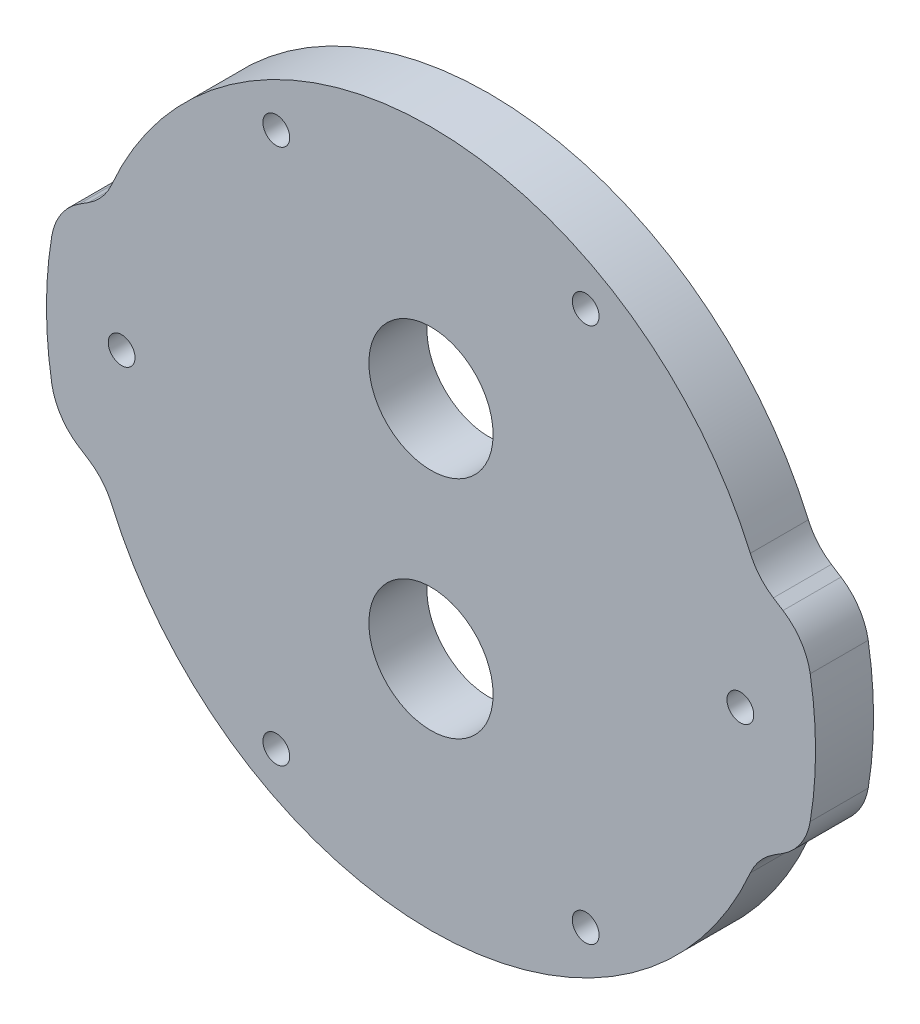
SolidWorks part; units mm, degrees
material "ABS PC"
ref_plane "Front Plane" through (0, 0, 0) normal (0, 0, 1) x (1, 0, 0)
ref_plane "Top Plane" through (0, 0, 0) normal (0, 1, 0) x (1, 0, 0)
ref_plane "Right Plane" through (0, 0, 0) normal (1, 0, 0) x (0, 0, -1)
sketch "Sketch1" plane through (0, 0, 0) normal (0, 0, 1) x (1, 0, 0)
  line L0 (-30.6713, 7.5) -> (-26.7681, 10)
  line L1 (-30.6713, -7.5) -> (-26.7681, -10)
  line L2 (30.6713, 7.5) -> (26.7681, 10)
  line L3 (30.6713, -7.5) -> (26.7681, -10)
  line L4 (0, 0) -> (-12.7, 21.997) construction
  line L5 (-12.7, 21.997) -> (-14.2875, 24.7467) construction
  line L6 (-25.4, 0) -> (0, 0) construction
  arc A0 (-26.7681, -10) -> (26.7681, -10) centre (0, 0) ccw
  circle A1 centre (-25.4, 0) radius 1.1
  circle A2 centre (-12.7, 21.997) radius 1.1
  circle A3 centre (12.7, 21.997) radius 1.1
  circle A4 centre (25.4, 0) radius 1.1
  circle A5 centre (12.7, -21.997) radius 1.1
  circle A6 centre (-12.7, -21.997) radius 1.1
  arc A7 (-30.6713, 7.5) -> (-30.6713, -7.5) centre (0, 0) ccw
  arc A8 (30.6713, 7.5) -> (30.6713, -7.5) centre (0, 0) cw
  arc A9 (26.7681, 10) -> (-26.7681, 10) centre (0, 0) ccw
  point P17 (0, 0)
  point P19 (-31.575, 0)
  point P24 (31.575, 0)
  dimension "D1" = 57.15
  dimension "D3" = 2.2
  dimension "D6" = 3
  dimension "D8" = 3
  dimension "D5" = 20
  dimension "D7" = 15
  dimension "D9" = 3.175
  dimension "D4" = 6
extrude "Boss-Extrude1" add sketch "Sketch1" along normal blind 4.7625
fillet "Fillet1" radius 5 8 edges at (26.7681, 10, 2.3813) (30.6713, 7.5, 2.3813) (30.6713, -7.5, 2.3813) (26.7681, -10, 2.3813) (-26.7681, -10, 2.3813) (-30.6713, -7.5, 2.3813) (-26.7681, 10, 2.3813) (-30.6713, 7.5, 2.3813)
sketch "Sketch2" plane through (0, 0, 0) normal (0, 0, 1) x (1, 0, 0)
  circle A0 centre (0, 0) radius 19 construction
  dimension "D1" = 38
sketch "Sketch3" plane through (0, 0, 4.7625) normal (0, 0, 1) x (1, 0, 0)
  line L0 (0, -9.25) -> (0, 0) construction
  line L1 (0, 0) -> (0, 9.25) construction
  line L2 (0, 0) -> (19, 0) construction
  circle A0 centre (0, -9.25) radius 5.1
  circle A1 centre (0, 9.25) radius 5.1
  circle A2 centre (0, 9.25) radius 9 construction
  circle A3 centre (0, -9.25) radius 9 construction
  circle A4 centre (0, 0) radius 19 construction
  dimension "D1" = 10.2
  dimension "D2" = 18
  dimension "D3" = 38
  dimension "D4" = 90
  dimension "D5" = 18.5
extrude "Cut-Extrude2" cut sketch "Sketch3" against normal through all contours A0 | A1
sketch "Sketch4" plane through (0, 0, 0) normal (0, 0, -1) x (-1, 0, 0)
  circle A0 centre (0, 0) radius 28.575
  circle A1 centre (0, 0) radius 19
  arc A2 (26.2186, 11.363) -> (-26.2186, 11.363) centre (0, 0) ccw construction
  dimension "D1" = 38
extrude "ANALYSIS-FIXTURE" [suppressed] add sketch "Sketch4" along normal blind 1
